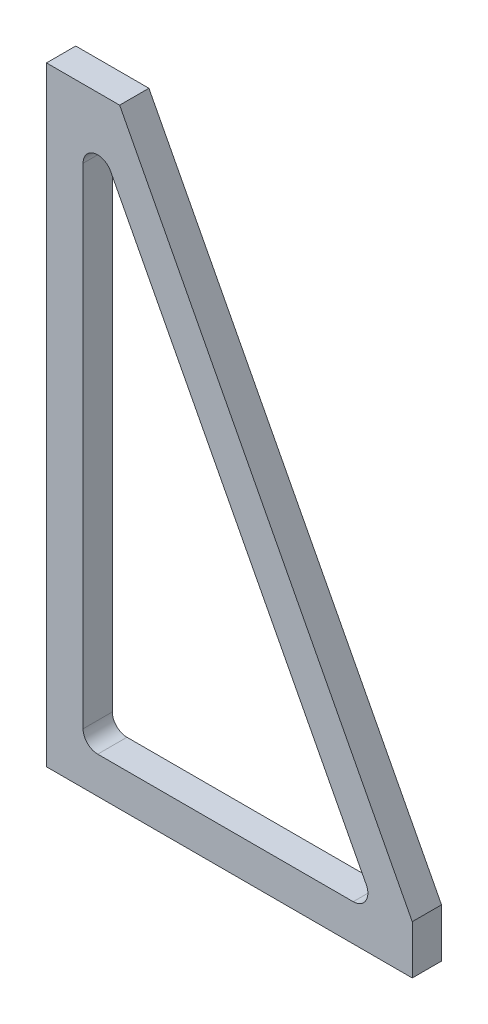
SolidWorks part; units mm, degrees
ref_plane "Front Plane" through (0, 0, 0) normal (0, 0, 1) x (1, 0, 0)
ref_plane "Top Plane" through (0, 0, 0) normal (0, 1, 0) x (1, 0, 0)
ref_plane "Right Plane" through (0, 0, 0) normal (1, 0, 0) x (0, 0, -1)
sketch "Sketch1" plane through (0, 0, 0) normal (0, 0, 1) x (1, 0, 0)
  line L0 (0, 0) -> (150, 0)
  line L1 (150, 0) -> (150, 20)
  line L2 (150, 20) -> (30, 250)
  line L3 (30, 250) -> (0, 250)
  line L4 (0, 250) -> (0, 0)
  line L5 (15, 221.8511) -> (15, 21)
  line L6 (21, 15) -> (125.7919, 15)
  line L8 (131.1114, 23.7754) -> (26.3195, 224.6265)
  line L10 (135, 16.3222) -> (20.9072, 235) construction
  line L11 (15, 15) -> (135, 15) construction
  line L12 (15, 235) -> (15, 15) construction
  line L13 (20.9072, 235) -> (15, 235) construction
  line L14 (135, 15) -> (135, 16.3222) construction
  arc A0 (131.1114, 23.7754) -> (125.7919, 15) centre (125.7919, 21) cw
  arc A1 (21, 15) -> (15, 21) centre (21, 21) cw
  arc A2 (15, 221.8511) -> (26.3195, 224.6265) centre (21, 221.8511) cw
  point P3 (206.4051, 20.5607)
  dimension "D6" = 6
  dimension "D1" = 30
  dimension "D2" = 250
  dimension "D3" = 20
  dimension "D4" = 150
  dimension "D5" = 15
extrude "Boss-Extrude2" add sketch "Sketch1" along normal blind 12
